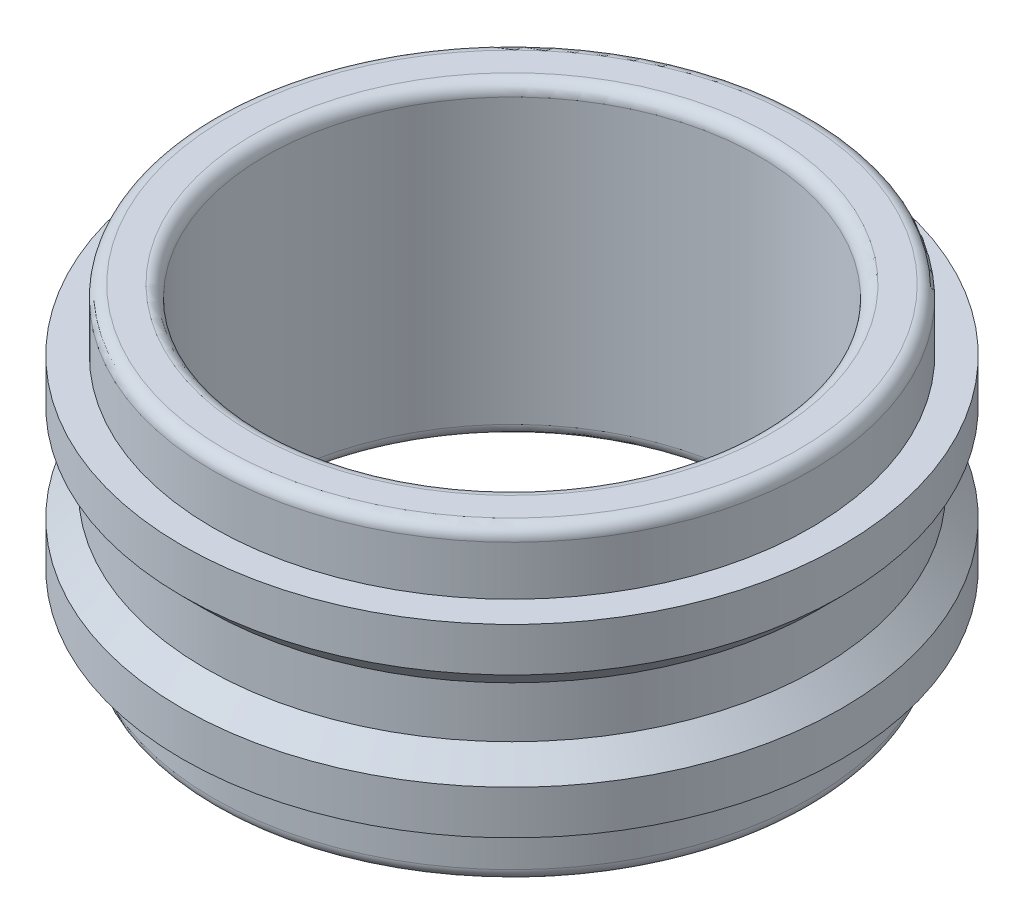
SolidWorks part; units mm, degrees
material "1060 Alloy"
ref_plane "Front" through (0, 0, 0) normal (0, 0, 1) x (1, 0, 0)
ref_plane "Top" through (0, 0, 0) normal (0, 1, 0) x (1, 0, 0)
ref_plane "Right" through (0, 0, 0) normal (1, 0, 0) x (0, 0, -1)
sketch "Çizim1" plane through (0, 0, 0) normal (0, 1, 0) x (1, 0, 0)
  circle A0 centre (0, 0) radius 4
  circle A1 centre (0, 0) radius 5.35
extrude "Yükseklik-Ekstrüzyon1" add sketch "Çizim1" along normal blind 5
sketch "Çizim4" plane through (0, 5, 0) normal (0, 1, 0) x (1, 0, 0)
  circle A0 centre (0, 0) radius 4.85
  circle A1 centre (0, 0) radius 5.35
extrude "Kes-Ekstrüzyon1" cut sketch "Çizim4" against normal blind 1
sketch "Çizim5" plane through (0, 0, 0) normal (0, 0, 1) x (1, 0, 0)
  line L3 (0, 0) -> (0, 5) construction
  line L4 (4, 5) -> (-4, 5) construction
pattern_linear "LÇoğaltma1" count 2 spacing 4 along (0, -1, 0) of "Kes-Ekstrüzyon1"
sketch "Çizim6" plane through (0, 0, 0) normal (0, 0, 1) x (1, 0, 0)
  line L0 (-5.5608, 3.5) -> (-4.975, 2.9142)
  line L1 (-4.975, 2.9142) -> (-4.975, 2.0858)
  line L2 (-5.5608, 1.5) -> (-4.975, 2.0858)
  line L4 (0, 0) -> (0, 5) construction
  line L5 (4, 5) -> (-4, 5) construction
  line L8 (-5.5608, 3.5) -> (-5.5608, 1.5)
revolve "Kes-Döndür1" cut sketch "Çizim6" angle 360 about L4
fillet "Radyus1" radius 0.2 4 edges at (0, 0, 4) (0, 0, 4.85) (0, 5, 4) (0, 5, 4.85)
